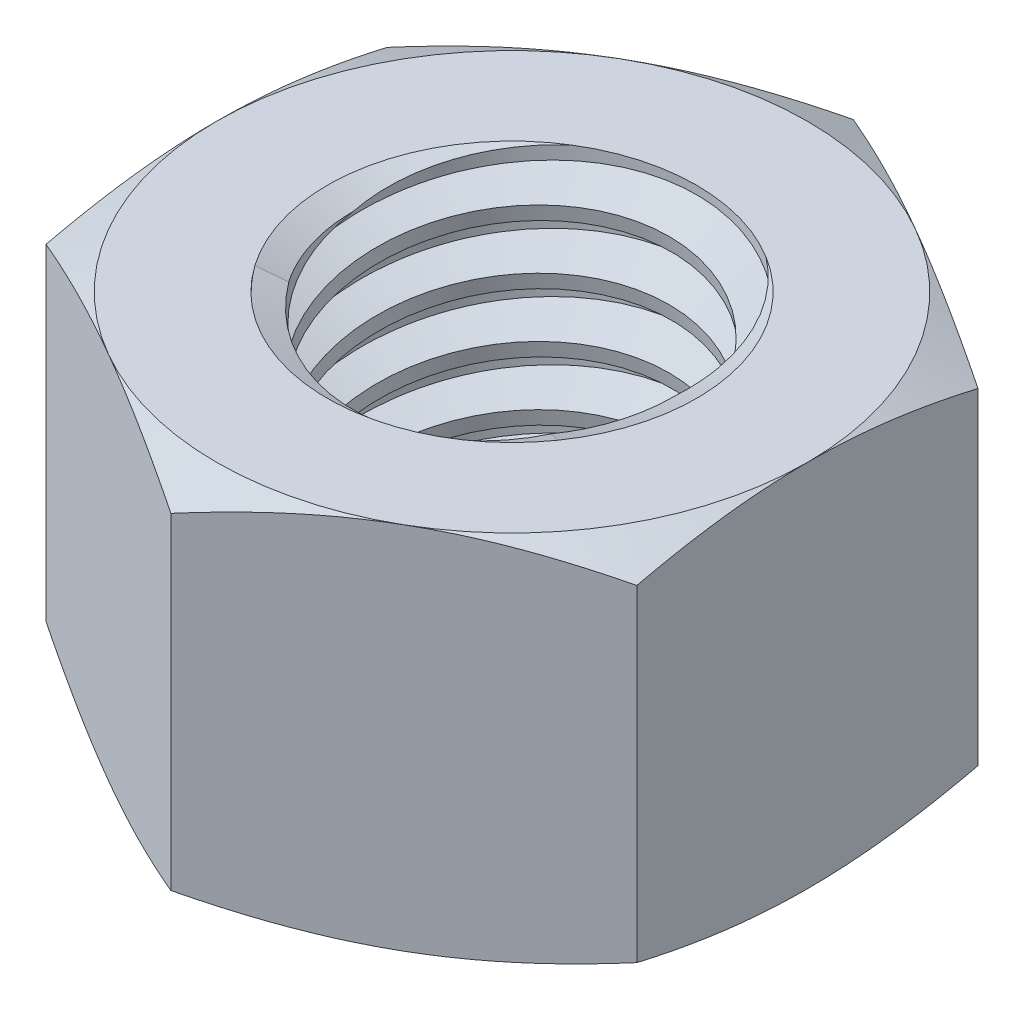
SolidWorks part; units mm, degrees
ref_plane "Front" through (0, 0, 0) normal (0, 0, 1) x (1, 0, 0)
ref_plane "Top" through (0, 0, 0) normal (0, 1, 0) x (1, 0, 0)
ref_plane "Right" through (0, 0, 0) normal (1, 0, 0) x (0, 0, -1)
sketch "Sketch1" plane through (0, 0, 0) normal (0, 1, 0) x (1, 0, 0)
  line L1 (0, 4.6188) -> (-4, 2.3094)
  line L2 (-4, 2.3094) -> (-4, -2.3094)
  line L3 (-4, -2.3094) -> (0, -4.6188)
  line L4 (0, -4.6188) -> (4, -2.3094)
  line L5 (4, -2.3094) -> (4, 2.3094)
  line L6 (4, 2.3094) -> (0, 4.6188)
  circle A0 centre (0, 0) radius 4 construction
  dimension "Hex Flats" = 8
extrude "Extrude1" add sketch "Sketch1" along normal mid plane 5
sketch "Sketch2" plane through (0, 0, 0) normal (1, 0, 0) x (0, 0, -1)
  line L0 (-2.5, -2.5) -> (-2.5, 2.5) construction
  line L1 (0, -2.5) -> (2.5, -2.5)
  line L2 (0, -2.5) -> (0, 2.5)
  line L3 (0, 2.5) -> (2.5, 2.5)
  line L4 (2.5, -2.5) -> (2.5, 2.5)
  line L5 (-2.3094, 2.5) -> (2.3094, 2.5) construction
  line L6 (-2.3094, -2.5) -> (2.3094, -2.5) construction
  line L7 (0, -5) -> (0, -2.5) construction
  dimension "Thread Dia" = 5
revolve "Revolve1" add sketch "Sketch2" angle 360 about L7
sketch "Sketch3" plane through (0, 0, 0) normal (1, 0, 0) x (0, 0, -1)
  line L0 (2.5, 2.5) -> (-2.5, 2.5) construction
  line L1 (-2.5, 2.5) -> (-2.5, 1.7) construction
  line L2 (-2.5, 1.7) -> (2.5, 2.5) construction
  line L3 (2.5, 2.5) -> (2.5158, 2.4013) construction
  line L4 (2.5158, 2.4013) -> (2.6264, 1.71)
  line L5 (2.6264, 1.71) -> (2.1593, 1.8885)
  line L6 (2.1593, 1.8885) -> (2.1277, 2.086)
  line L7 (2.1277, 2.086) -> (2.5158, 2.4013)
  line L8 (2.1435, 1.9872) -> (2.5711, 2.0557) construction
  line L9 (2.5, 2.5) -> (2.5, 2.0443) construction
  line L10 (2.5, 2.0443) -> (-2.5, 1.2443) construction
  line L11 (-2.5, 1.2443) -> (-2.5, 1.7) construction
  line L12 (-0.1369, 2.5) -> (0.1369, 0.7886) construction
  line L13 (-2.5, -2.5) -> (-2.5, 2.5) construction
  line L14 (0, 2.5) -> (2.5, 2.5) construction
  line L15 (2.5, -2.5) -> (2.5, 2.5) construction
  line L16 (0, 0) -> (0, 2.5) construction
  line L17 (-2.5158, 2.4013) -> (-2.6264, 1.71) construction
  line L18 (-2.1277, 2.086) -> (-2.5158, 2.4013) construction
  line L19 (-2.1593, 1.8885) -> (-2.1277, 2.086) construction
  line L20 (-2.6264, 1.71) -> (-2.1593, 1.8885) construction
  line L21 (0.1369, 2.5) -> (-0.1369, 0.7886) construction
  point P13 (0, 1.6443)
  dimension "D1" = 0.1
  dimension "D2" = 0.2
  dimension "Thread Pitch" = 0.8
  dimension "D4" = 60
  dimension "D5" = 0.8
revolve "Cut-Revolve1" cut sketch "Sketch3" angle 360 about L12
pattern_linear "LPattern1" count 6 spacing 0.8 along (0, -1, 0) count 2 spacing 0.8 along (0, 1, 0) of "Cut-Revolve1"
sketch "Sketch4" plane through (0, 0, 0) normal (1, 0, 0) x (0, 0, -1)
  line L0 (0, 2.5) -> (2.5, 2.5)
  line L1 (2.5, 2.5) -> (2.1277, 2.3264)
  line L2 (2.1277, 2.3264) -> (2.1277, -2.3264)
  line L3 (2.1277, -2.3264) -> (2.5, -2.5)
  line L4 (2.5, -2.5) -> (0, -2.5)
  line L5 (0, -2.5) -> (0, 2.5)
  line L6 (2.5, -2.5) -> (2.5, 2.5) construction
  line L7 (0, 2.5) -> (2.5, 2.5) construction
  line L8 (0, -2.5) -> (2.5, -2.5) construction
  line L9 (0, -2.5) -> (0, 2.5) construction
  line L10 (0, 2.5) -> (0, 2.9108) construction
  dimension "D1" = 25
revolve "Cut-Revolve2" cut sketch "Sketch4" angle 360 about L10
combine bodies "Combine1" operation type subtract main body 112 bodies to subtract 111
sketch "Sketch5" plane through (0, 0, 0) normal (1, 0, 0) x (0, 0, -1)
  line L0 (0, -2.5) -> (4, -2.5)
  line L1 (4, -2.5) -> (4.6188, -2.2114)
  line L2 (4.6188, -2.2114) -> (4.6188, 2.2114)
  line L3 (4.6188, 2.2114) -> (4, 2.5)
  line L4 (0, 2.5) -> (0, 3.77)
  line L5 (0, 3.77) -> (5.8888, 3.77)
  line L6 (5.8888, 3.77) -> (5.8888, -3.77)
  line L7 (5.8888, -3.77) -> (0, -3.77)
  line L8 (0, -3.77) -> (0, -2.5)
  line L9 (4, 2.5) -> (4, -2.5) construction
  line L11 (0, -2.5) -> (2.5, -2.5) construction
  line L12 (4, 2.5) -> (0, 2.5)
  line L13 (4.6188, 0) -> (5.8888, 0) construction
  line L14 (4.6188, 2.5) -> (4.6188, -2.5) construction
  line L15 (0, -2.5) -> (0, 2.5) construction
  line L17 (0, 0) -> (4, 0) construction
  line L22 (0, 2.5) -> (2.5, 2.5) construction
  dimension "D1" = 25
  dimension "D2" = 1.27
  dimension "D3" = 5
revolve "Cut-Revolve3" cut sketch "Sketch5" angle 360 about L15
equation "\"D1@Sketch3\"=\"Thread Pitch@Sketch3\"/8"
equation "\"D2@Sketch3\"=\"Thread Pitch@Sketch3\"/4"
equation "\"D5@Sketch3\"=\"Thread Pitch@Sketch3\""
equation "\"D4@LPattern1\"=\"Thread Pitch@Sketch3\""
equation "\"D3@LPattern1\"=\"Thread Pitch@Sketch3\""
equation "\"D1@LPattern1\"=\"Height@Extrude1\"/\"Thread Pitch@Sketch3\""
